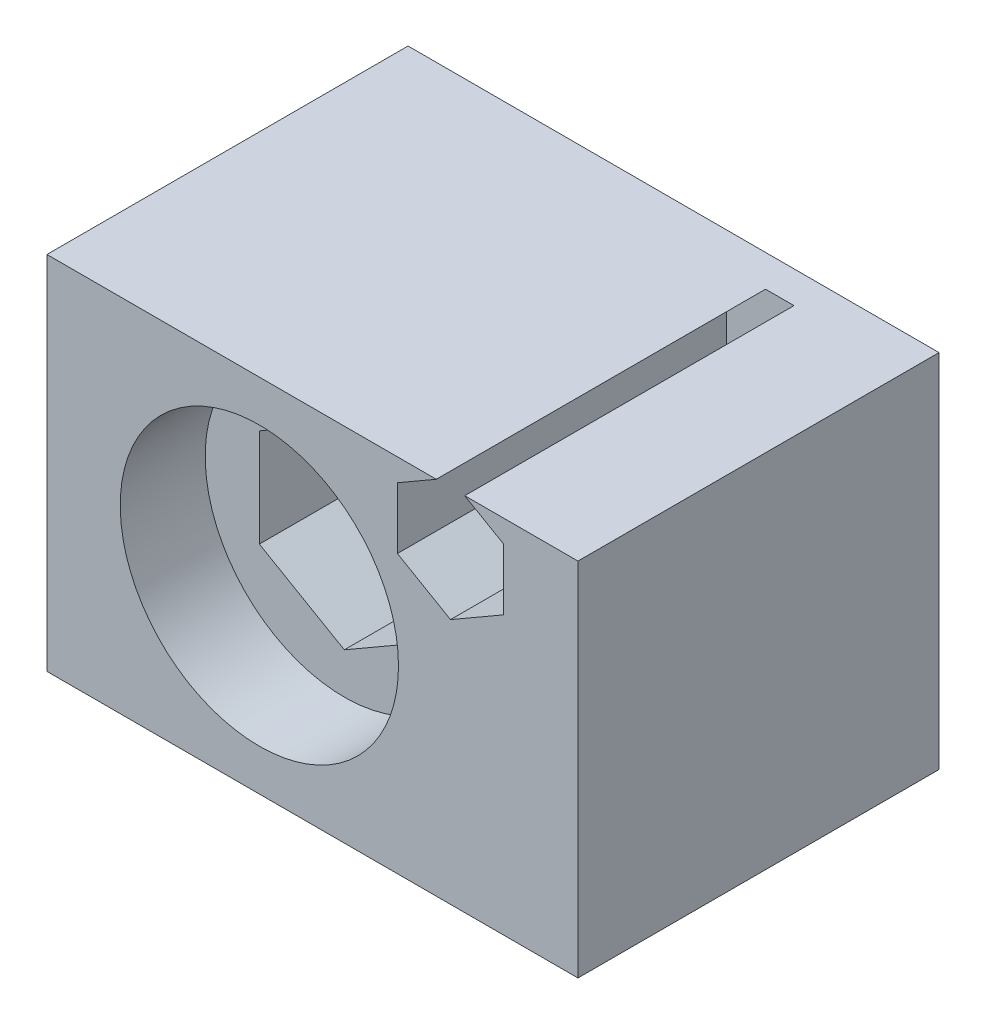
SolidWorks part; units mm, degrees
ref_plane "Front" through (0, 0, 0) normal (0, 0, 1) x (1, 0, 0)
ref_plane "Top" through (0, 0, 0) normal (0, 1, 0) x (1, 0, 0)
ref_plane "Right" through (0, 0, 0) normal (1, 0, 0) x (0, 0, -1)
sketch "草图1" plane through (0, 0, 0) normal (1, 0, 0) x (0, 0, -1)
  line L1 (0, 0) -> (18, 0)
  line L2 (0, 0) -> (0, 18)
  line L3 (0, 18) -> (18, 18)
  line L4 (18, 0) -> (18, 18)
  dimension "D1" = 18
  dimension "D2" = 18
extrude "凸台-拉伸1" add sketch "草图1" along normal blind 25
sketch "草图2" plane through (0, 0, 0) normal (0, 0, 1) x (1, 0, 0)
  line L0 (0, 9) -> (25, 9) construction
  line L1 (0, 18) -> (0, 0) construction
  line L2 (25, 18) -> (25, 0) construction
  circle A0 centre (10, 9) radius 6.55
  dimension "D1" = 13.1
  dimension "D2" = 10
extrude "切除-拉伸1" cut sketch "草图2" against normal blind 4.5
sketch "草图3" plane through (0, 0, -4.5) normal (0, 0, 1) x (1, 0, 0)
  line L1 (10, 13.6188) -> (6, 11.3094)
  line L2 (6, 11.3094) -> (6, 6.6906)
  line L3 (6, 6.6906) -> (10, 4.3812)
  line L4 (10, 4.3812) -> (14, 6.6906)
  line L5 (14, 6.6906) -> (14, 11.3094)
  line L6 (14, 11.3094) -> (10, 13.6188)
  circle A0 centre (10, 9) radius 4 construction
  dimension "D1" = 8
extrude "切除-拉伸2" cut sketch "草图3" against normal offset from surface (11.7 mm away) 1.8 up to face at (12.5, 9, -18)
sketch "草图4" plane through (0, 0, 0) normal (0, 0, 1) x (1, 0, 0)
  line L0 (25, 18) -> (25, 0) construction
  line L1 (19, 17.8868) -> (16.5, 16.4434)
  line L2 (16.5, 16.4434) -> (16.5, 13.5566)
  line L3 (16.5, 13.5566) -> (19, 12.1132)
  line L4 (19, 12.1132) -> (21.5, 13.5566)
  line L5 (21.5, 13.5566) -> (21.5, 16.4434)
  line L6 (21.5, 16.4434) -> (19, 17.8868)
  line L7 (25, 18) -> (0, 18) construction
  circle A0 centre (19, 15) radius 1.5 construction
  circle A1 centre (19, 15) radius 2.5 construction
  dimension "D1" = 3
  dimension "D2" = 5
  dimension "D3" = 6
  dimension "D4" = 3
extrude "切除-拉伸3" cut sketch "草图4" against normal blind 16
sketch "草图5" plane through (0, 0, 0) normal (0, 0, 1) x (1, 0, 0)
  line L0 (25, 18) -> (0, 18) construction
  line L1 (0.4, 17.6) -> (24.6, 17.6)
  line L2 (0.4, 17.6) -> (0.4, 0.4)
  line L3 (0.4, 0.4) -> (24.6, 0.4)
  line L4 (24.6, 17.6) -> (24.6, 0.4)
  line L5 (0, 18) -> (0, 0) construction
  line L6 (25, 18) -> (25, 0) construction
  line L7 (25, 0) -> (0, 0) construction
  line L9 (0, 0) -> (25, 0)
  line L10 (0, 0) -> (0, 18)
  line L11 (0, 18) -> (25, 18)
  line L12 (25, 0) -> (25, 18)
  dimension "D1" = 0.4
  dimension "D2" = 0.4
  dimension "D3" = 0.4
  dimension "D4" = 0.4
extrude "切除-拉伸4" [suppressed] cut sketch "草图5" against normal through all
sketch "草图6" plane through (0, 0, 0) normal (-1, 0, 0) x (0, 0, 1)
  line L1 (-18, 18) -> (0, 18)
  line L2 (-18, 18) -> (-18, 0)
  line L3 (-18, 0) -> (0, 0)
  line L4 (0, 18) -> (0, 0)
  line L5 (-17.5, 17.5) -> (-0.5, 17.5)
  line L6 (-17.5, 17.5) -> (-17.5, 0.5)
  line L7 (-17.5, 0.5) -> (-0.5, 0.5)
  line L8 (-0.5, 17.5) -> (-0.5, 0.5)
  dimension "D1" = 0.5
  dimension "D2" = 0.5
  dimension "D3" = 0.5
  dimension "D4" = 0.5
extrude "切除-拉伸5" cut sketch "草图6" against normal through all
